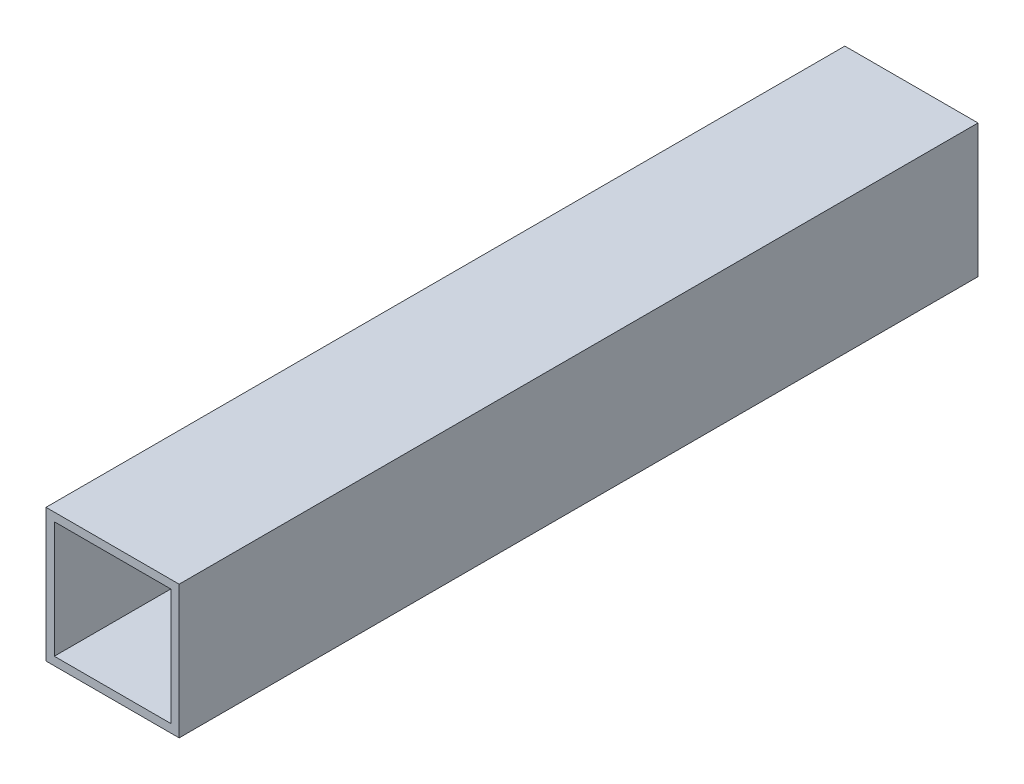
SolidWorks part; units mm, degrees
ref_plane "Front Plane" through (0, 0, 0) normal (0, 0, 1) x (1, 0, 0)
ref_plane "Top Plane" through (0, 0, 0) normal (0, 1, 0) x (1, 0, 0)
ref_plane "Right Plane" through (0, 0, 0) normal (1, 0, 0) x (0, 0, -1)
sketch "Sketch1" plane through (0, 0, 0) normal (0, 0, 1) x (1, 0, 0)
  line L0 (-11.1125, 11.1125) -> (11.1125, 11.1125)
  line L2 (-12.7, 12.7) -> (12.7, 12.7)
  line L3 (-12.7, 12.7) -> (-12.7, -12.7)
  line L4 (-12.7, -12.7) -> (12.7, -12.7)
  line L5 (12.7, 12.7) -> (12.7, -12.7)
  line L10 (11.1125, 11.1125) -> (11.1125, -11.1125)
  line L11 (-11.1125, -11.1125) -> (11.1125, -11.1125)
  line L12 (-11.1125, 11.1125) -> (-11.1125, -11.1125)
  point P12 (0, 12.7)
  point P14 (12.7, 0)
  dimension "Wall Thickness" = 1.5875
  dimension "Outside Width" = 25.4
  dimension "Outside Height" = 25.4
  dimension "Inside Height" = 22.225
  dimension "Inside Width" = 22.225
sketch "Sketch2" plane through (0, 0, 0) normal (1, 0, 0) x (0, 0, -1)
  line L0 (76.2, 0) -> (-76.2, 0)
  point P4 (0, 0)
  point P7 (-76.2, 0)
  point P10 (76.2, 0)
  dimension "Length" = 152.4
sketch "Sketch3" plane through (0, 0, 0) normal (0, 0, 1) x (1, 0, 0)
  line L21 (12.7, 12.7) -> (-12.7, 12.7)
  line L22 (12.7, -12.7) -> (12.7, 12.7)
  line L23 (-12.7, -12.7) -> (12.7, -12.7)
  line L24 (-12.7, 12.7) -> (-12.7, -12.7)
  line L25 (12.7, 12.7) -> (-12.7, 12.7)
  line L26 (12.7, -12.7) -> (12.7, 12.7)
  line L27 (-12.7, -12.7) -> (12.7, -12.7)
  line L28 (-12.7, 12.7) -> (-12.7, -12.7)
  line L29 (11.1125, 11.1125) -> (-11.1125, 11.1125)
  line L30 (11.1125, -11.1125) -> (11.1125, 11.1125)
  line L31 (-11.1125, -11.1125) -> (11.1125, -11.1125)
  line L32 (-11.1125, 11.1125) -> (-11.1125, -11.1125)
  line L33 (11.1125, 11.1125) -> (-11.1125, 11.1125)
  line L34 (11.1125, -11.1125) -> (11.1125, 11.1125)
  line L35 (-11.1125, -11.1125) -> (11.1125, -11.1125)
  line L36 (-11.1125, 11.1125) -> (-11.1125, -11.1125)
  dimension "D1" = 0
  dimension "D2" = 0
extrude "Boss-Extrude1" add sketch "Sketch3" along normal up to vertex (76.2 mm away) and the other way up to vertex (76.2 mm away) up to point (0, 0, 76.2) other way up to point (0, 0, -76.2)
sketch "Drawing Reference" plane through (0, 0, 0) normal (1, 0, 0) x (0, 0, -1)
  line L0 (-76.2, 0) -> (76.2, 0) construction
  line L1 (0, -12.7) -> (0, 12.7) construction
  line L2 (-76.2, -12.7) -> (76.2, -12.7) construction
  line L5 (-76.2, 12.7) -> (76.2, 12.7) construction
  point P7 (-57.912, 0)
  point P8 (57.912, 0)
  dimension "D1" = 18.288
equation "\"D1@Drawing Reference\"=\"Outside Width@Sketch1\" * 0.72"
